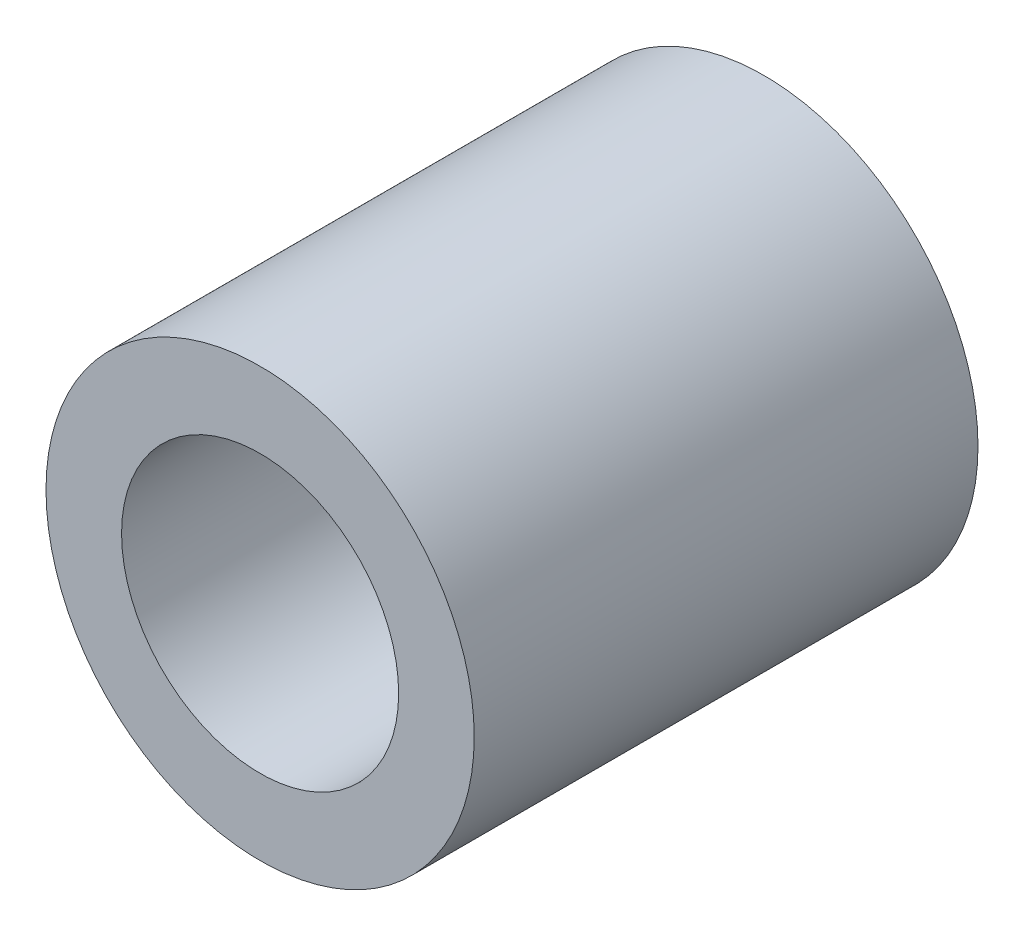
SolidWorks part; units mm, degrees
ref_plane "Front Plane" through (0, 0, 0) normal (0, 0, 1) x (1, 0, 0)
ref_plane "Top Plane" through (0, 0, 0) normal (0, 1, 0) x (1, 0, 0)
ref_plane "Right Plane" through (0, 0, 0) normal (1, 0, 0) x (0, 0, -1)
sketch "Sketch1" plane through (0, 0, 0) normal (0, 0, 1) x (1, 0, 0)
  circle A0 centre (0, 0) radius 4.25
  circle A1 centre (0, 0) radius 2.75
  dimension "D1" = 5.5
  dimension "D2" = 1.5
extrude "Boss-Extrude1" add sketch "Sketch1" along normal blind 10
